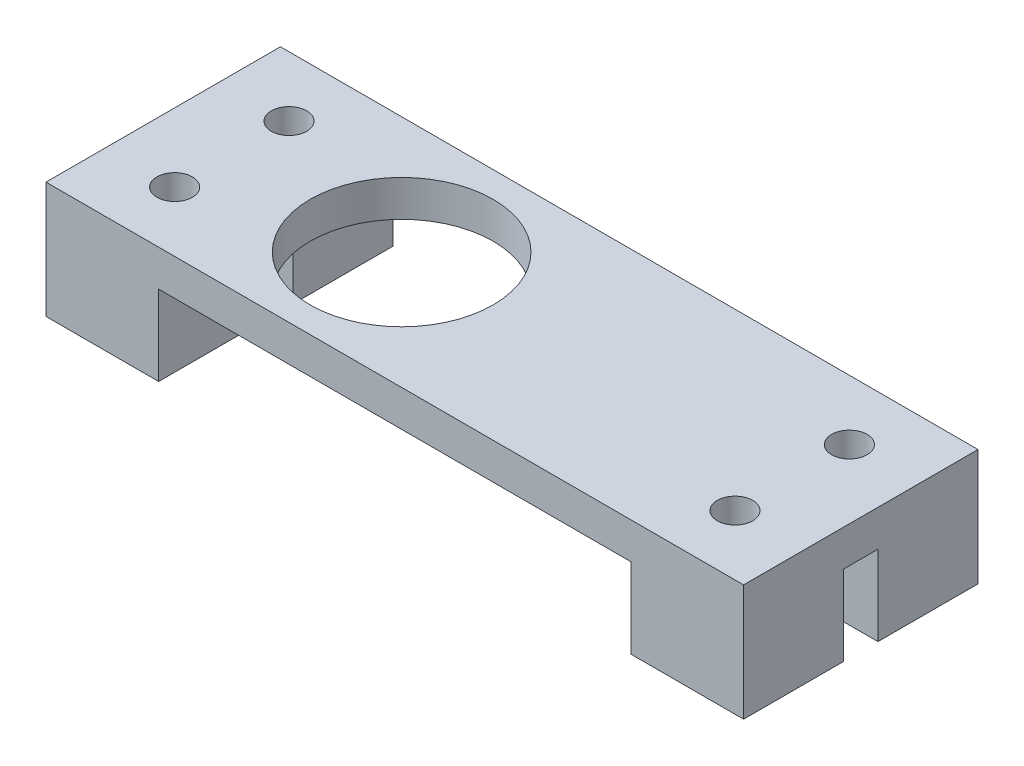
SolidWorks part; units mm, degrees
ref_plane "Front Plane" through (0, 0, 0) normal (0, 0, 1) x (1, 0, 0)
ref_plane "Top Plane" through (0, 0, 0) normal (0, 1, 0) x (1, 0, 0)
ref_plane "Right Plane" through (0, 0, 0) normal (1, 0, 0) x (0, 0, -1)
sketch "Sketch2" plane through (0, 0, 0) normal (0, 1, 0) x (1, 0, 0)
  line L0 (-24.5, 5) -> (-24.5, -5) construction
  line L1 (-30.5, 10.25) -> (30.5, 10.25)
  line L2 (-30.5, 10.25) -> (-30.5, -10.25)
  line L3 (-30.5, -10.25) -> (30.5, -10.25)
  line L4 (30.5, 10.25) -> (30.5, -10.25)
  line L5 (-30.5, 10.25) -> (30.5, -10.25) construction
  line L6 (-30.5, -10.25) -> (30.5, 10.25) construction
  line L7 (-24.5, -5) -> (24.5, -5) construction
  line L8 (24.5, -5) -> (24.5, 5) construction
  line L9 (24.5, 5) -> (-24.5, 5) construction
  line L10 (-20.65, 10.25) -> (-20.65, -10.25) construction
  line L15 (20.65, 10.25) -> (20.65, -10.25) construction
  line L16 (-20.65, 0) -> (20.65, 0) construction
  circle A0 centre (-9.65, 0) radius 8
  circle A1 centre (-24.5, 5) radius 1.55
  circle A2 centre (-24.5, -5) radius 1.55
  circle A3 centre (24.5, 5) radius 1.55
  circle A4 centre (24.5, -5) radius 1.55
  point P0 (0, 0)
  point P16 (-24.5, 0)
  point P17 (0, 5)
  point P27 (0, 0)
  dimension "D1" = 16
  dimension "D2" = 3.1
  dimension "D9" = 41.3
  dimension "D10" = 11
  dimension "D3" = 6
  dimension "D4" = 10
  dimension "D5" = 49
  dimension "D6" = 20.5
extrude "Boss-Extrude1" add sketch "Sketch2" along normal blind 3.175
sketch "Sketch3" plane through (0, 0, 0) normal (0, -1, 0) x (1, 0, 0)
  line L0 (-20.65, 10.25) -> (-20.65, -10.25)
  line L1 (-30.5, 10.25) -> (30.5, 10.25) construction
  line L2 (-30.5, -10.25) -> (30.5, -10.25) construction
  line L3 (-20.65, -10.25) -> (-30.5, -10.25)
  line L4 (-30.5, -10.25) -> (-30.5, 10.25)
  line L5 (-30.5, 10.25) -> (-20.65, 10.25)
  line L6 (20.65, 10.25) -> (20.65, -10.25)
  line L7 (20.65, -10.25) -> (30.5, -10.25)
  line L8 (30.5, -10.25) -> (30.5, 10.25)
  line L9 (30.5, 10.25) -> (20.65, 10.25)
  line L10 (-30.5, 10.25) -> (30.5, 10.25) construction
  line L12 (-30.5, 1.5) -> (-20.65, 1.5)
  line L13 (-30.5, 1.5) -> (-30.5, -1.5)
  line L14 (-30.5, -1.5) -> (-20.65, -1.5)
  line L15 (-20.65, 1.5) -> (-20.65, -1.5)
  line L16 (20.65, 1.5) -> (30.5, 1.5)
  line L17 (20.65, 1.5) -> (20.65, -1.5)
  line L18 (20.65, -1.5) -> (30.5, -1.5)
  line L19 (30.5, 1.5) -> (30.5, -1.5)
  circle A0 centre (-24.5, -5) radius 1.55
  circle A1 centre (-24.5, 5) radius 1.55
  circle A2 centre (24.5, -5) radius 1.55
  circle A3 centre (24.5, 5) radius 1.55
  point P43 (20.65, 0)
  point P44 (-20.65, 0)
  circle M5 centre (24.5, 5) radius 1.55
  circle M6 centre (24.5, -5) radius 1.55
  circle M7 centre (-24.5, 5) radius 1.55
  circle M8 centre (-24.5, -5) radius 1.55
  line M13 (30.5, -10.25) -> (30.5, 10.25)
  line M14 (30.5, 10.25) -> (-30.5, 10.25)
  line M15 (-30.5, 10.25) -> (-30.5, -10.25)
  line M16 (-30.5, -10.25) -> (30.5, -10.25)
  dimension "D1" = 3
extrude "Boss-Extrude2" add sketch "Sketch3" along normal blind 7 contours L12 L0 M15 M14 M7 | L14 L0 M15 M16 M8 | L6 L16 L8 M14 M5 | L18 L6 M16 M13 M6
